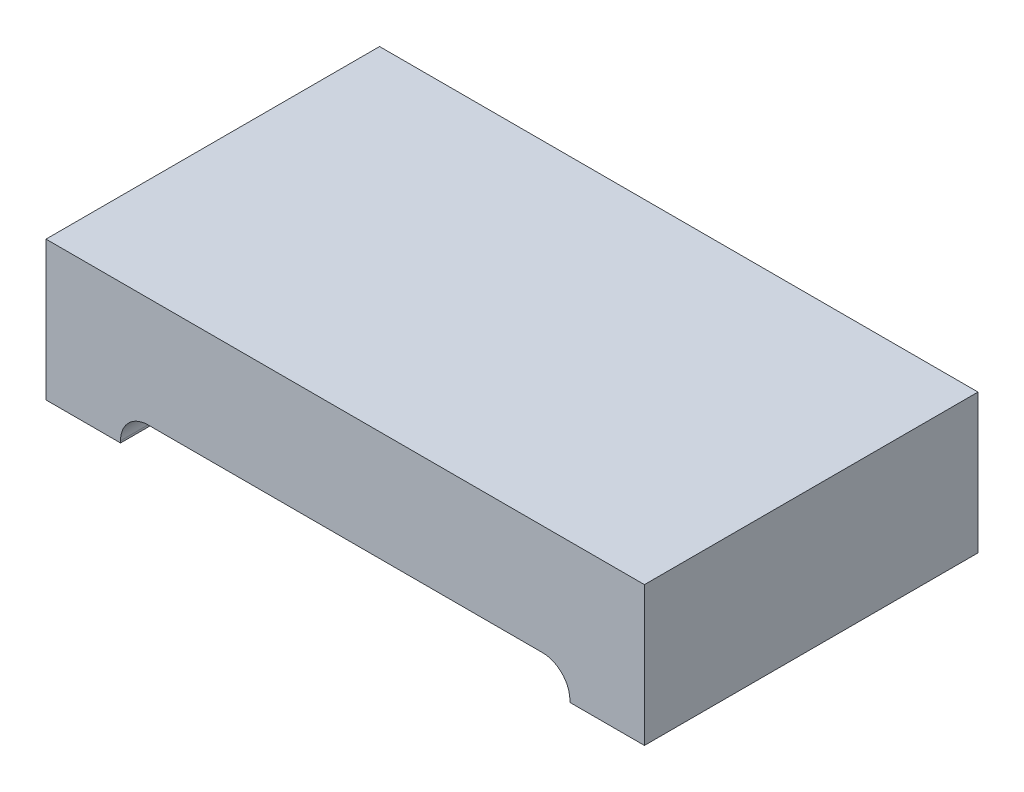
SolidWorks part; units mm, degrees
ref_plane "Front Plane" through (0, 0, 0) normal (0, 0, 1) x (1, 0, 0)
ref_plane "Top Plane" through (0, 0, 0) normal (0, 1, 0) x (1, 0, 0)
ref_plane "Right Plane" through (0, 0, 0) normal (1, 0, 0) x (0, 0, -1)
sketch "Sketch1" plane through (0, 0, 0) normal (0, 1, 0) x (1, 0, 0)
  line L1 (-1.525, -0.85) -> (1.525, -0.85)
  line L2 (-1.525, -0.85) -> (-1.525, 0.85)
  line L3 (-1.525, 0.85) -> (1.525, 0.85)
  line L4 (1.525, -0.85) -> (1.525, 0.85)
  line L5 (-1.525, -0.85) -> (1.525, 0.85) construction
  line L6 (-1.525, 0.85) -> (1.525, -0.85) construction
  point P0 (0, 0)
  dimension "D1" = 3.05
  dimension "D2" = 1.7
extrude "Boss-Extrude1" add sketch "Sketch1" along normal blind 0.71
sketch "Sketch2" plane through (0, 0, 0) normal (0, 0, 1) x (1, 0, 0)
  line L0 (-1.525, 0.71) -> (-1.525, 0) construction
  line L1 (-1.145, 0) -> (1.145, 0)
  line L2 (-1.145, 0) -> (-1.145, 0.01)
  line L3 (-1.005, 0.15) -> (1.005, 0.15)
  line L4 (1.145, 0) -> (1.145, 0.01)
  arc A0 (1.005, 0.15) -> (1.145, 0.01) centre (1.005, 0.01) cw
  arc A1 (-1.145, 0.01) -> (-1.005, 0.15) centre (-1.005, 0.01) cw
  point P4 (0, 0)
  point P10 (1.145, 0.15)
  dimension "D3" = 0.14
  dimension "D1" = 0.38
  dimension "D2" = 0.15
extrude "Cut-Extrude1" cut sketch "Sketch2" against normal through all both and the other way through all
